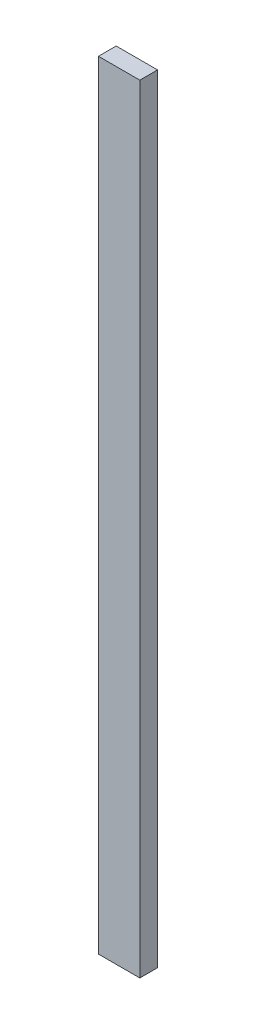
SolidWorks part; units mm, degrees
material "Oak"
ref_plane "Front Plane" through (0, 0, 0) normal (0, 0, 1) x (1, 0, 0)
ref_plane "Top Plane" through (0, 0, 0) normal (0, 1, 0) x (1, 0, 0)
ref_plane "Right Plane" through (0, 0, 0) normal (1, 0, 0) x (0, 0, -1)
sketch "Sketch1" plane through (0, 0, 0) normal (0, 1, 0) x (1, 0, 0)
  line L1 (-44.45, -19.05) -> (44.45, -19.05)
  line L2 (-44.45, -19.05) -> (-44.45, 19.05)
  line L3 (-44.45, 19.05) -> (44.45, 19.05)
  line L4 (44.45, -19.05) -> (44.45, 19.05)
  line L5 (-44.45, -19.05) -> (44.45, 19.05) construction
  line L6 (-44.45, 19.05) -> (44.45, -19.05) construction
  point P0 (0, 0)
  dimension "D1" = 38.1
  dimension "D2" = 88.9
extrude "Boss-Extrude1" add sketch "Sketch1" along normal blind 1670.05 contours L3 L4 L1 L2
